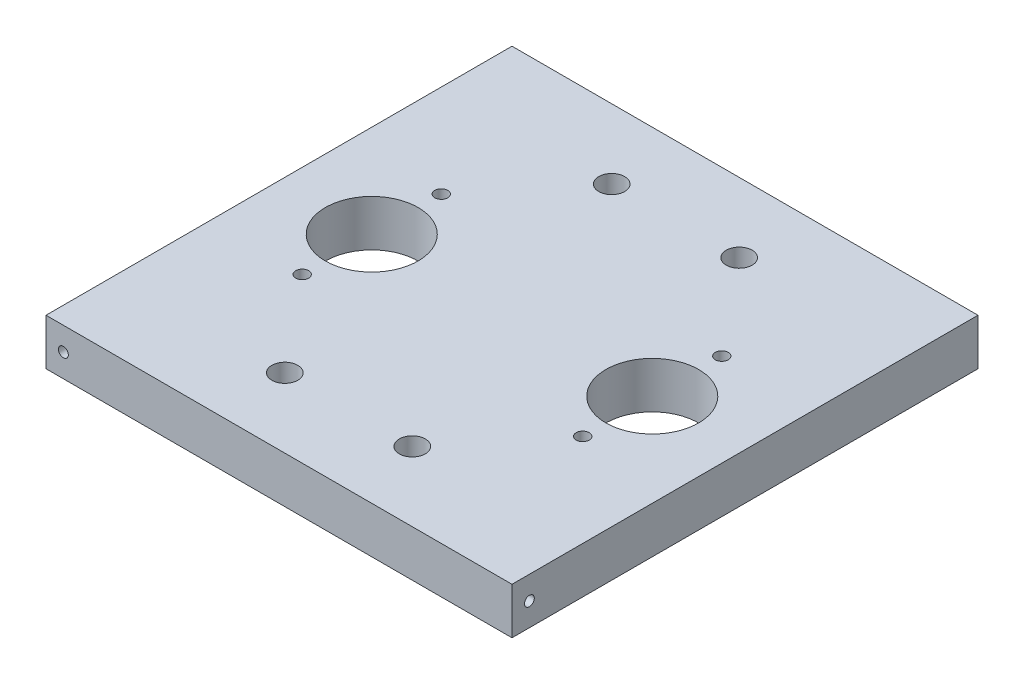
SolidWorks part; units mm, degrees
material "6061-T6 (SS)"
ref_plane "Front" through (0, 0, 0) normal (0, 0, 1) x (1, 0, 0)
ref_plane "Top" through (0, 0, 0) normal (0, 1, 0) x (1, 0, 0)
ref_plane "Right" through (0, 0, 0) normal (1, 0, 0) x (0, 0, -1)
sketch "Sketch1" plane through (0, 0, 0) normal (0, 1, 0) x (1, 0, 0)
  line L1 (0, 0) -> (127.635, 0)
  line L2 (0, 0) -> (0, 127.635)
  line L3 (0, 127.635) -> (127.635, 127.635)
  line L4 (127.635, 0) -> (127.635, 127.635)
  dimension "D1" = 127.635
  dimension "D2" = 127.635
extrude "Main Plate" add sketch "Sketch1" along normal blind 12.7
sketch "Sketch2" plane through (0, 12.7, 0) normal (0, 1, 0) x (1, 0, 0)
  line L0 (0, 127.635) -> (0, 0) construction
  line L1 (127.635, 127.635) -> (0, 127.635) construction
  circle A0 centre (46.355, 108.585) radius 3.556
  dimension "D1" = 7.112
  dimension "D2" = 46.355
  dimension "D3" = 19.05
extrude "U-Bolt Hole" cut sketch "Sketch2" against normal blind 12.7
pattern_linear "U-Bolt Pattern" count 2 spacing 34.925 along (1, 0, 0) count 2 spacing 89.535 along (0, 0, 1) of "U-Bolt Hole"
sketch "Sketch3" plane through (0, 12.7, 0) normal (0, 1, 0) x (1, 0, 0)
  line L0 (0, 127.635) -> (0, 0) construction
  line L1 (0, 0) -> (127.635, 0) construction
  circle A0 centre (25.4, 44.7675) radius 1.778
  dimension "D1" = 3.556
  dimension "D2" = 25.4
  dimension "D3" = 44.7675
extrude "Raptor Bolt Hole" cut sketch "Sketch3" against normal blind 12.7
pattern_linear "Raptor Bolt Pattern" count 2 spacing 38.1 along (0, 0, -1) count 2 spacing 76.835 along (1, 0, 0) of "Raptor Bolt Hole"
sketch "Sketch4" plane through (0, 12.7, 0) normal (0, 1, 0) x (1, 0, 0)
  line L0 (0, 127.635) -> (0, 0) construction
  line L1 (127.635, 127.635) -> (0, 127.635) construction
  circle A0 centre (25.4, 63.8175) radius 12.7
  dimension "D1" = 25.4
  dimension "D2" = 63.8175
  dimension "D3" = 25.4
extrude "Co2 Cylinder Hole" cut sketch "Sketch4" against normal blind 12.7
pattern_linear "Co2 Pattern" count 2 spacing 76.835 along (1, 0, 0) of "Co2 Cylinder Hole"
sketch "Sketch5" plane through (0, 0, 0) normal (0, 0, 1) x (1, 0, 0)
  line L0 (0, 12.7) -> (0, 0) construction
  line L1 (0, 0) -> (127.635, 0) construction
  circle A0 centre (4.7625, 6.35) radius 1.3526
  dimension "D1" = 2.7051
  dimension "D2" = 4.7625
  dimension "D3" = 6.35
extrude "Frame attachment hole 1" cut sketch "Sketch5" against normal blind 12.7
sketch "Sketch6" plane through (0, 0, 0) normal (-1, 0, 0) x (0, 0, 1)
  line L2 (-127.635, 0) -> (0, 0) construction
  line L3 (-127.635, 12.7) -> (-127.635, 0) construction
  circle A0 centre (-122.8725, 6.35) radius 1.3525
  dimension "D1" = 2.7051
  dimension "D2" = 6.35
  dimension "D3" = 4.7625
extrude "Frame attachment hole 2" cut sketch "Sketch6" against normal blind 12.7
sketch "Sketch7" plane through (0, 0, -127.635) normal (0, 0, -1) x (-1, 0, 0)
  line L2 (-127.635, 0) -> (0, 0) construction
  line L3 (-127.635, 12.7) -> (-127.635, 0) construction
  circle A0 centre (-122.8725, 6.35) radius 1.3526
  dimension "D1" = 2.7051
  dimension "D2" = 6.35
  dimension "D3" = 4.7625
extrude "Frame attachment hole 3" cut sketch "Sketch7" against normal blind 12.7
sketch "Sketch8" plane through (127.635, 0, 0) normal (1, 0, 0) x (0, 0, -1)
  line L2 (0, 0) -> (127.635, 0) construction
  line L3 (0, 12.7) -> (0, 0) construction
  circle A0 centre (4.7625, 6.35) radius 1.3526
  dimension "D1" = 2.7051
  dimension "D2" = 6.35
  dimension "D3" = 4.7625
extrude "Frame attachment hole 4" cut sketch "Sketch8" against normal blind 12.7
